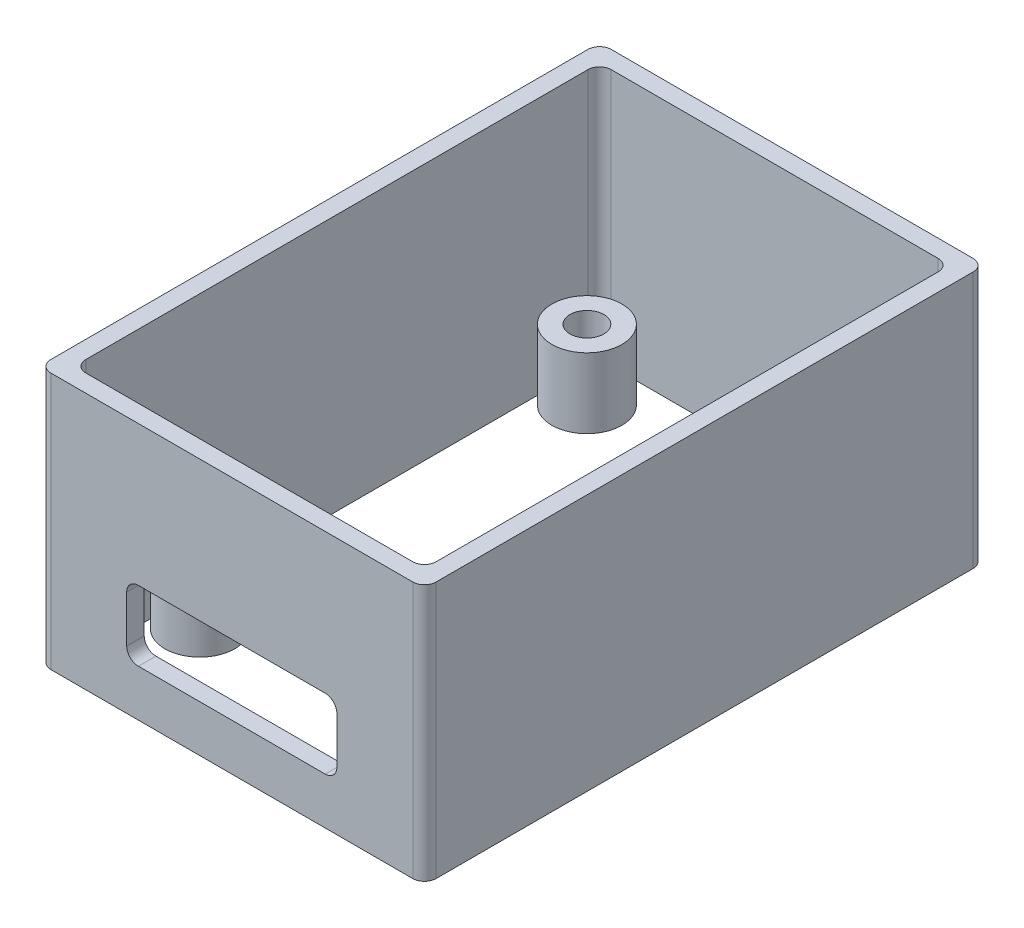
SolidWorks part; units mm, degrees
ref_plane "Front Plane" through (0, 0, 0) normal (0, 0, 1) x (1, 0, 0)
ref_plane "Top Plane" through (0, 0, 0) normal (0, 1, 0) x (1, 0, 0)
ref_plane "Right Plane" through (0, 0, 0) normal (1, 0, 0) x (0, 0, -1)
sketch "Sketch1" plane through (0, 0, 0) normal (0, 1, 0) x (1, 0, 0)
  line L1 (-16.5, 24) -> (16.5, 24)
  line L2 (-16.5, 24) -> (-16.5, -24)
  line L3 (-16.5, -24) -> (16.5, -24)
  line L4 (16.5, 24) -> (16.5, -24)
  line L5 (-16.5, 24) -> (16.5, -24) construction
  line L6 (-16.5, -24) -> (16.5, 24) construction
  point P0 (0, 0)
  dimension "D1" = 48
  dimension "D2" = 33
extrude "Boss-Extrude1" add sketch "Sketch1" along normal blind 22 contours L4 L3 L2 L1
sketch "Sketch2" plane through (0, 22, 0) normal (0, 1, 0) x (1, 0, 0)
  line L0 (-16.5, 24) -> (16.5, -24) construction
  line L2 (-15, 22.5) -> (15, 22.5)
  line L3 (-15, 22.5) -> (-15, -22.5)
  line L4 (-15, -22.5) -> (15, -22.5)
  line L5 (15, 22.5) -> (15, -22.5)
  line L6 (-15, 22.5) -> (15, -22.5) construction
  line L7 (-15, -22.5) -> (15, 22.5) construction
  point P4 (0, 0)
  dimension "D1" = 45
  dimension "D2" = 30
extrude "Cut-Extrude1" cut sketch "Sketch2" against normal blind 25
sketch "Sketch4" plane through (0, 2, 0) normal (0, 1, 0) x (1, 0, 0)
  line L0 (-15, 22.5) -> (15, -22.5) construction
  line L1 (15, -22.5) -> (15, 22.5) construction
  line L3 (-10.16, 16.575) -> (10.16, 16.575) construction
  line L4 (-10.16, 16.575) -> (-10.16, -16.575) construction
  line L5 (-10.16, -16.575) -> (10.16, -16.575) construction
  line L6 (10.16, 16.575) -> (10.16, -16.575) construction
  line L7 (-10.16, 16.575) -> (10.16, -16.575) construction
  line L8 (-10.16, -16.575) -> (10.16, 16.575) construction
  circle A1 centre (-10.16, 16.575) radius 3
  circle A3 centre (10.16, -16.575) radius 3
  circle A5 centre (10.16, 16.575) radius 3
  circle A7 centre (-10.16, -16.575) radius 3
  point P5 (0, 0)
  dimension "D1" = 33.15
  dimension "D2" = 20.32
extrude "Boss-Extrude5" add sketch "Sketch4" along normal blind 6
sketch "Sketch11" plane through (0, 0, 24) normal (0, 0, 1) x (1, 0, 0)
  line L0 (0, 0) -> (0, 22) construction
  line L2 (-16.5, 22) -> (16.5, 22) construction
  line L3 (9, 4) -> (-9, 4)
  line L4 (9, 4) -> (9, 10)
  line L5 (9, 10) -> (-9, 10)
  line L6 (-9, 4) -> (-9, 10)
  line L7 (7.16, 8) -> (-7.16, 8) construction
  dimension "D1" = 18
  dimension "D2" = 6
extrude "Cut-Extrude5" cut sketch "Sketch11" against normal blind 1.5
fillet "Fillet5" radius 1 8 edges at (16.5, 11, -24) (15, 11, -22.5) (-16.5, 11, -24) (-15, 11, -22.5) (-16.5, 11, 24) (-15, 11, 22.5) (15, 11, 22.5) (16.5, 11, 24)
hole_wizard "CSK for M2.5 Flat Head Machine Screw1" positions "Sketch12" profile "Sketch13" countersink size "M2.5" standard "ANSI Metric" end condition through all
sketch "Sketch12" plane through (0, 0, 0) normal (0, -1, 0) x (-1, 0, 0)
  point P0 (10.16, -16.575)
  point P3 (-10.16, -16.575)
  point P6 (-10.16, 16.575)
  point P9 (10.16, 16.575)
sketch "Sketch13" plane through (-10.16, 0, 16.575) normal (1, 0, 0) x (0, 0, -1)
  line L0 (0, 0) -> (0, 22)
  line L1 (0, 22) -> (1.45, 22)
  line L2 (1.45, 22) -> (1.45, 1.3)
  line L3 (1.45, 1.3) -> (2.75, 0)
  line L5 (2.75, 0) -> (0, 0)
  line L6 (-1.45, 1.3) -> (-2.75, 0) construction
  line L11 (0, -6.35) -> (0, 107.95) construction
  dimension "Thru Hole Dia." = 2.9
  dimension "Thru Hole Depth" = 22
  dimension "Near C'Sink Dia." = 5.5
  dimension "Near C'Sink Angle" = 90
fillet "Fillet6" radius 1 4 edges at (9, 4, 23.25) (9, 10, 23.25) (-9, 10, 23.25) (-9, 4, 23.25)
